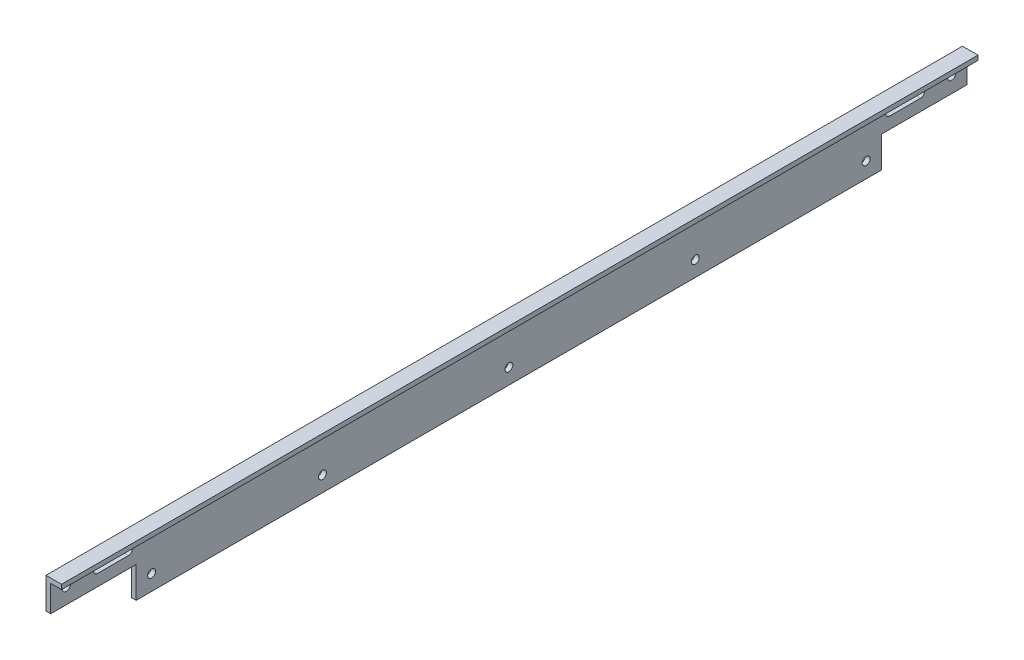
SolidWorks part; units mm, degrees
ref_plane "Front Plane" through (0, 0, 0) normal (0, 0, 1) x (1, 0, 0)
ref_plane "Top Plane" through (0, 0, 0) normal (0, 1, 0) x (1, 0, 0)
ref_plane "Right Plane" through (0, 0, 0) normal (1, 0, 0) x (0, 0, -1)
sketch "Sketch1" plane through (0, 0, 0) normal (0, 0, 1) x (1, 0, 0)
  line L0 (0, 0) -> (0, 40)
  line L1 (0, 40) -> (10, 40)
  line L2 (10, 40) -> (10, 37)
  line L3 (10, 37) -> (3, 37)
  line L4 (3, 37) -> (3, 0)
  line L5 (3, 0) -> (0, 0)
  dimension "D1" = 3
  dimension "D2" = 10
  dimension "D3" = 40
extrude "Boss-Extrude1" add sketch "Sketch1" along normal blind 590
sketch "Sketch2" plane through (3, 0, 0) normal (1, 0, 0) x (0, 0, -1)
  line L0 (-295, 102.8094) -> (-295, -73.9754) construction
  line L1 (-590, 0) -> (-590, 37) construction
  line L3 (0, 0) -> (0, 37) construction
  line L4 (-590, 0) -> (0, 0) construction
  circle A0 centre (-525, 10) radius 2.55
  circle A1 centre (-295, 10) radius 2.55
  circle A4 centre (-415, 10) radius 2.55
  circle A5 centre (-175, 10) radius 2.55
  circle A6 centre (-65, 10) radius 2.55
  dimension "D1" = 10
  dimension "D2" = 65
  dimension "D3" = 295
  dimension "D4" = 65
  dimension "D5" = 175
  dimension "D6" = 175
  dimension "D7" = 5.1
extrude "Cut-Extrude3" cut sketch "Sketch2" against normal up to next
sketch "Sketch5" plane through (3, 0, 0) normal (1, 0, 0) x (0, 0, -1)
  line L0 (-590, 20) -> (-535, 20)
  line L2 (-535, 20) -> (-535, 0)
  line L3 (-590, 0) -> (0, 0) construction
  line L4 (-535, 0) -> (-590, 0)
  line L5 (-590, 0) -> (-590, 20)
  line L6 (-295, 61.7719) -> (-295, -21.9854) construction
  line L7 (0, 0) -> (0, 37) construction
  line L8 (-55, 0) -> (0, 0)
  line L9 (0, 0) -> (0, 20)
  line L10 (0, 20) -> (-55, 20)
  line L11 (-55, 20) -> (-55, 0)
  dimension "D1" = 55
  dimension "D2" = 20
  dimension "D3" = 295
extrude "Cut-Extrude5" cut sketch "Sketch5" against normal up to next
sketch "Sketch6" plane through (0, 0, 0) normal (-1, 0, 0) x (0, 0, 1)
  line L0 (30, 30) -> (50, 30) construction
  line L1 (30, 32.55) -> (50, 32.55)
  line L2 (30, 27.45) -> (50, 27.45)
  line L3 (0, 40) -> (0, 20) construction
  line L4 (590, 40) -> (0, 40) construction
  line L5 (295, 65.3992) -> (295, -22.8252) construction
  line L6 (590, 40) -> (590, 20) construction
  line L7 (560, 30) -> (540, 30) construction
  line L8 (560, 32.55) -> (540, 32.55)
  line L9 (560, 27.45) -> (540, 27.45)
  arc A0 (30, 32.55) -> (30, 27.45) centre (30, 30) ccw
  arc A1 (50, 27.45) -> (50, 32.55) centre (50, 30) ccw
  circle A2 centre (10, 30) radius 2.55
  arc A3 (560, 32.55) -> (560, 27.45) centre (560, 30) cw
  arc A4 (540, 27.45) -> (540, 32.55) centre (540, 30) cw
  circle A5 centre (580, 30) radius 2.55
  point P2 (40, 30)
  point P19 (550, 30)
  dimension "D1" = 30
  dimension "D2" = 10
  dimension "D5" = 10
  dimension "D7" = 5.1
  dimension "D8" = 2.55
  dimension "D3" = 20
  dimension "D4" = 10
  dimension "D6" = 295
extrude "Cut-Extrude6" cut sketch "Sketch6" against normal up to next
